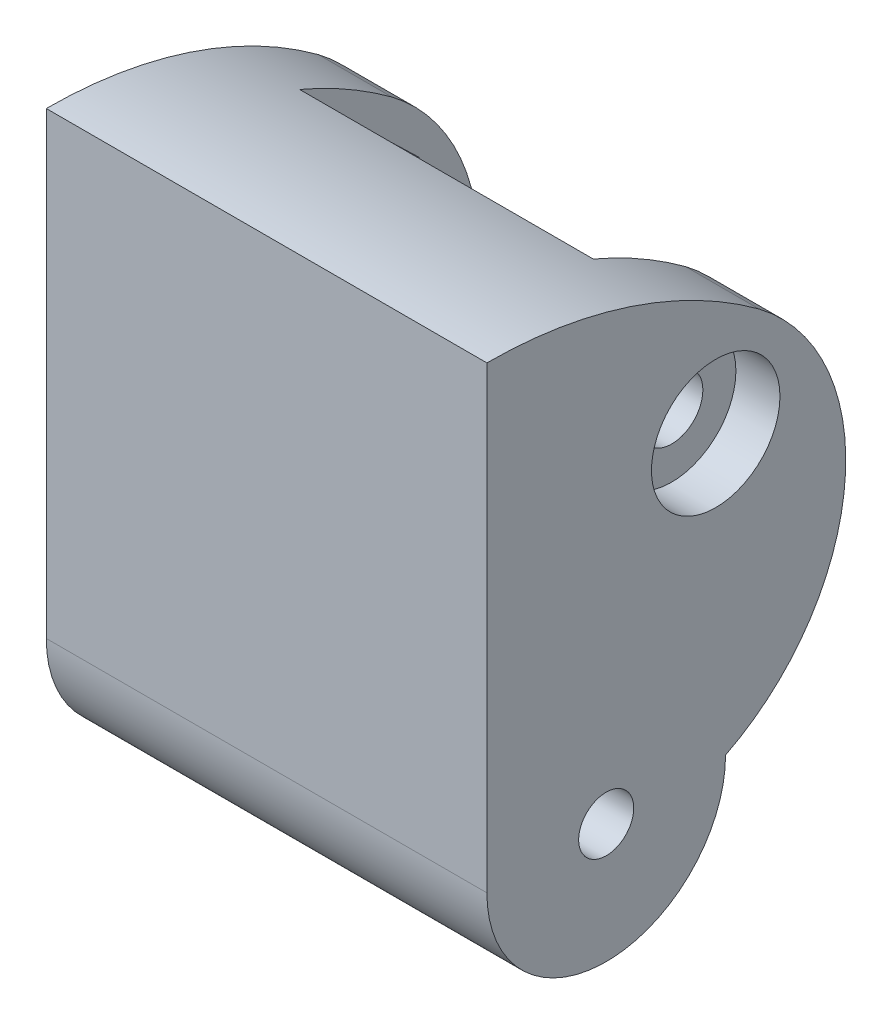
SolidWorks part; units mm, degrees
ref_plane "Płaszczyzna przednia" through (0, 0, 0) normal (0, 0, 1) x (1, 0, 0)
ref_plane "Płaszczyzna górna" through (0, 0, 0) normal (0, 1, 0) x (1, 0, 0)
ref_plane "Płaszczyzna prawa" through (0, 0, 0) normal (1, 0, 0) x (0, 0, -1)
sketch "Szkic5" plane through (0, 0, 0) normal (1, 0, 0) x (0, 0, -1)
  line L0 (-12.9082, 21.2755) -> (-12.9082, -3.7245)
  line L2 (-12.9082, 21.2755) -> (-12.9082, 5.6894)
  arc A0 (-12.9082, -3.7245) -> (0.0918, -3.7245) centre (-6.4082, -3.7245) ccw
  arc A1 (-12.9082, 21.2755) -> (1.9156, 16.4065) centre (-12.9082, -3.7245) cw
  arc A2 (0.0918, -3.7245) -> (1.9156, 16.4065) centre (-5.2674, 6.9091) ccw
  circle A4 centre (-6.4082, -3.7245) radius 1.5
  dimension "D2" = 13
  dimension "D3" = 3
  dimension "D1" = 25
extrude "Dodanie-wyciągnięcie2" add sketch "Szkic5" along normal blind 24 contours A0 A2 A1 L0
hole_wizard "Pogłębienie walcowe pod M3 wkręt do części metalowych z łbem stożkowym ściętym1" positions "Szkic13" profile "Szkic12" counterbore size "M3" standard "Ansi Metric" end condition through all
sketch "Szkic13" plane through (24, 0, 0) normal (1, 0, 0) x (0, 0, -1)
  point P2 (-0.4436, 11.7153)
sketch "Szkic12" plane through (24, 11.7153, 0.4436) normal (0, 1, 0) x (0, 0, -1)
  line L0 (0, 0) -> (0, 24)
  line L1 (0, 24) -> (1.7, 24)
  line L3 (1.7, 24) -> (1.7, 2.4)
  line L4 (1.7, 2.4) -> (3.5, 2.4)
  line L5 (3.5, 2.4) -> (3.5, 0)
  line L7 (3.5, 0) -> (0, 0)
  line L11 (0, -6.35) -> (0, 107.95) construction
  dimension "Średnica otworu na wylot" = 3.4
  dimension "Głębokość otworu na wylot" = 24
  dimension "Średnica pogłębienia walcowego" = 7
  dimension "Głębokość pogłębienia walcowego" = 2.4
sketch "Szkic14" plane through (0, 0, 0) normal (0, 0, 1) x (1, 0, 0)
  line L1 (24, 21.2755) -> (0, 21.2755) construction
  line L4 (12, 21.2755) -> (12, -3.7245) construction
  line L5 (24, -3.7245) -> (0, -3.7245) construction
  line L9 (20, 19.2755) -> (4, 19.2755)
  line L10 (20, 19.2755) -> (20, 2.2755)
  line L11 (20, 2.2755) -> (4, 2.2755)
  line L12 (4, 19.2755) -> (4, 2.2755)
  dimension "D3" = 17
  dimension "D4" = 16
extrude "Wytnij-wyciągnięcie1" cut sketch "Szkic14" against normal blind 24 and the other way blind 9
sketch "Szkic18" plane through (0, 0, 0) normal (-1, 0, 0) x (0, 0, 1)
  line L19 (1.4122, 7.8343) -> (4.2889, 10.6136)
  line L20 (4.2889, 10.6136) -> (3.3204, 14.4945)
  line L21 (3.3204, 14.4945) -> (-0.5249, 15.5962)
  line L22 (-0.5249, 15.5962) -> (-3.4016, 12.817)
  line L23 (-3.4016, 12.817) -> (-2.4331, 8.936)
  line L24 (-2.4331, 8.936) -> (1.4122, 7.8343)
  circle A0 centre (0.4436, 11.7153) radius 4 construction
extrude "Wytnij-wyciągnięcie2" cut sketch "Szkic18" against normal blind 8 contours L19 L20 L21 L22 L23 L24
